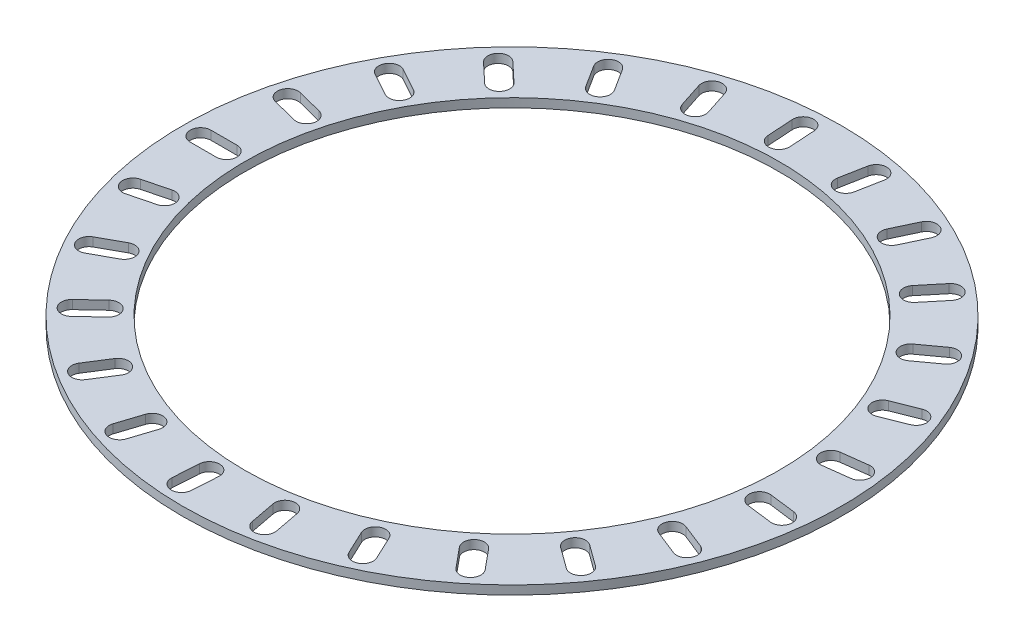
SolidWorks part; units mm, degrees
material "Copper"
ref_plane "Front Plane" through (0, 0, 0) normal (0, 0, 1) x (1, 0, 0)
ref_plane "Top Plane" through (0, 0, 0) normal (0, 1, 0) x (1, 0, 0)
ref_plane "Right Plane" through (0, 0, 0) normal (1, 0, 0) x (0, 0, -1)
sketch "Sketch1" plane through (0, 0, 0) normal (0, 1, 0) x (1, 0, 0)
  line L0 (0, 0) -> (-51.8433, 0) construction
  circle A0 centre (0, 0) radius 31.77
  circle A1 centre (0, 0) radius 25.77
  dimension "D1" = 63.54
  dimension "D2" = 6
extrude "Boss-Extrude1" add sketch "Sketch1" along normal blind 0.85
sketch "Sketch3" plane through (0, 0.85, 0) normal (0, 1, 0) x (1, 0, 0)
  line L0 (0, 0) -> (-50.1119, 0) construction
  line L2 (-30.02, 0) -> (-27.52, 0) construction
  line L3 (-30.02, 1) -> (-27.52, 1)
  line L4 (-30.02, -1) -> (-27.52, -1)
  circle A2 centre (0, 0) radius 28.77 construction
  arc A3 (-30.02, 1) -> (-30.02, -1) centre (-30.02, 0) ccw
  arc A4 (-27.52, -1) -> (-27.52, 1) centre (-27.52, 0) ccw
  point P3 (-28.77, 0)
  dimension "D2" = 1
  dimension "D3" = 57.54
  dimension "D1" = 2.5
extrude "Cut-Extrude1" cut sketch "Sketch3" against normal through all
pattern_circular "CirPattern1" count 25 over 360 about axis through (0, 0, 0) along (0, 1, 0) of "Cut-Extrude1"
